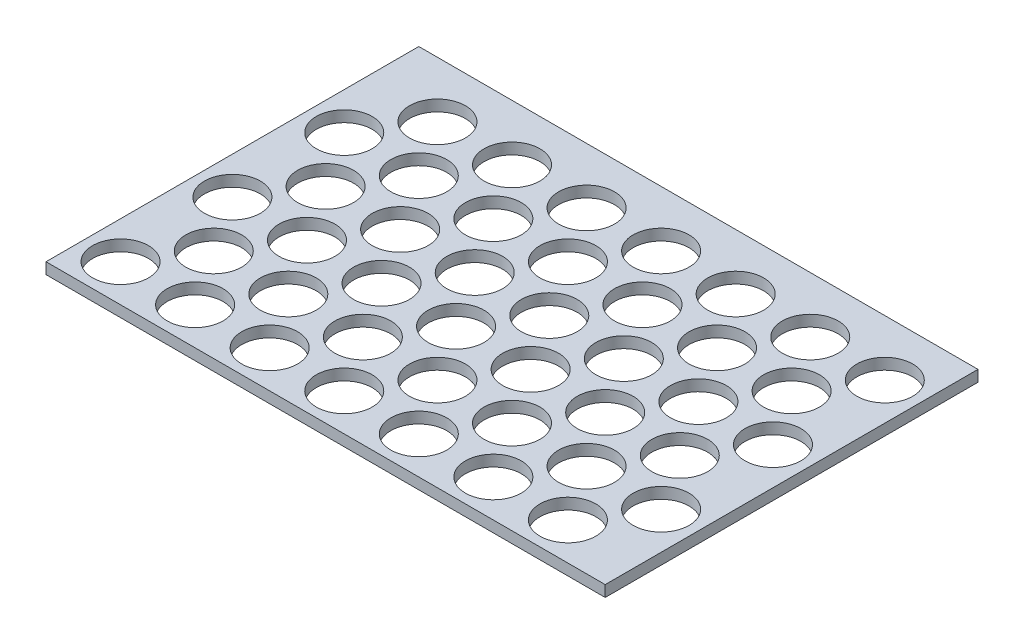
SolidWorks part; units mm, degrees
ref_plane "Спереди" through (0, 0, 0) normal (0, 0, 1) x (1, 0, 0)
ref_plane "Сверху" through (0, 0, 0) normal (0, 1, 0) x (1, 0, 0)
ref_plane "Справа" through (0, 0, 0) normal (1, 0, 0) x (0, 0, -1)
sketch "Эскиз1" plane through (0, 0, 0) normal (0, 1, 0) x (1, 0, 0)
  line L1 (0, 0) -> (150, 0)
  line L2 (0, 0) -> (0, 100)
  line L3 (0, 100) -> (150, 100)
  line L4 (150, 0) -> (150, 100)
extrude "Бобышка-Вытянуть1" add sketch "Эскиз1" along normal blind 3
sketch "Эскиз2" plane through (0, 3, 0) normal (0, 1, 0) x (1, 0, 0)
  circle A0 centre (10, 10) radius 7.5
  circle A1 centre (20, 25) radius 7.5
  circle A2 centre (30, 10) radius 7.5
  circle A3 centre (40, 25) radius 7.5
  circle A4 centre (50, 10) radius 7.5
  circle A5 centre (60, 25) radius 7.5
  circle A6 centre (70, 10) radius 7.5
  circle A7 centre (80, 25) radius 7.5
  circle A8 centre (90, 10) radius 7.5
  circle A9 centre (100, 25) radius 7.5
  circle A10 centre (110, 10) radius 7.5
  circle A11 centre (120, 25) radius 7.5
  circle A12 centre (130, 10) radius 7.5
  circle A13 centre (140, 25) radius 7.5
  circle A14 centre (30, 40) radius 7.5
  circle A15 centre (40, 55) radius 7.5
  circle A16 centre (50, 40) radius 7.5
  circle A17 centre (60, 55) radius 7.5
  circle A18 centre (70, 40) radius 7.5
  circle A19 centre (80, 55) radius 7.5
  circle A20 centre (90, 40) radius 7.5
  circle A21 centre (100, 55) radius 7.5
  circle A22 centre (110, 40) radius 7.5
  circle A23 centre (120, 55) radius 7.5
  circle A24 centre (130, 40) radius 7.5
  circle A25 centre (140, 55) radius 7.5
  circle A26 centre (30, 70) radius 7.5
  circle A27 centre (40, 85) radius 7.5
  circle A28 centre (50, 70) radius 7.5
  circle A29 centre (60, 85) radius 7.5
  circle A30 centre (70, 70) radius 7.5
  circle A31 centre (80, 85) radius 7.5
  circle A32 centre (90, 70) radius 7.5
  circle A33 centre (100, 85) radius 7.5
  circle A34 centre (110, 70) radius 7.5
  circle A35 centre (120, 85) radius 7.5
  circle A36 centre (130, 70) radius 7.5
  circle A37 centre (140, 85) radius 7.5
  circle A38 centre (10, 40) radius 7.5
  circle A39 centre (20, 55) radius 7.5
  circle A40 centre (10, 70) radius 7.5
  circle A41 centre (20, 85) radius 7.5
  dimension "D1" = 7
  dimension "D2" = 3
extrude "Вырез-Вытянуть1" cut sketch "Эскиз2" against normal through all
